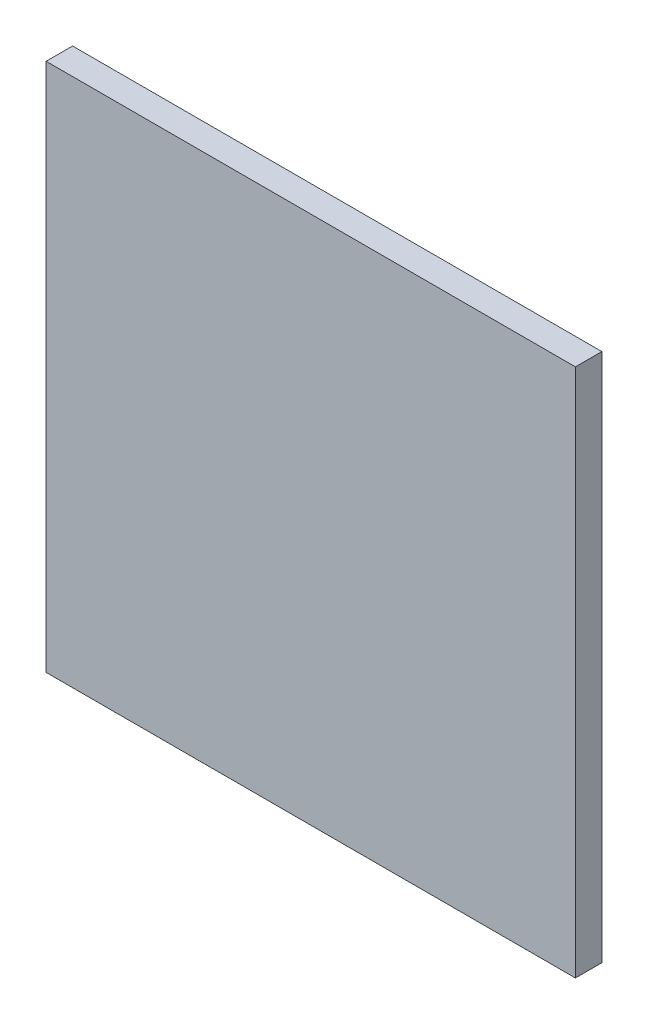
SolidWorks part; units mm, degrees
ref_plane "Front Plane" through (0, 0, 0) normal (1, 0, 0) x (0, 1, 0)
ref_plane "Top Plane" through (0, 0, 0) normal (0, 0, 1) x (0, 1, 0)
ref_plane "Right Plane" through (0, 0, 0) normal (0, 1, 0) x (-1, 0, 0)
sketch "Sketch1" plane through (0, 0, 0) normal (0, 0, 1) x (0, 1, 0)
  line L1 (0, 0) -> (127, 0)
  line L2 (0, 0) -> (0, 127)
  line L3 (0, 127) -> (127, 127)
  line L4 (127, 0) -> (127, 127)
  dimension "D1" = 127
  dimension "D2" = 127
extrude "Boss-Extrude1" add sketch "Sketch1" along normal blind 6.35
